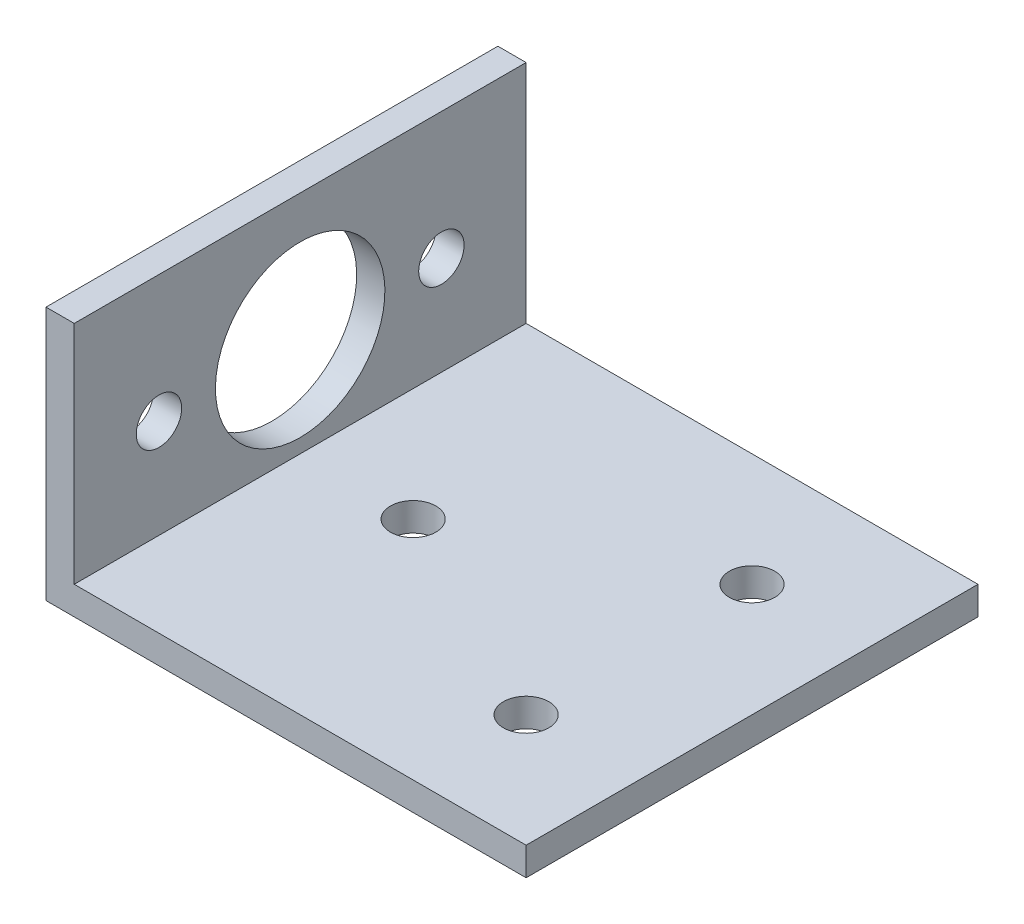
SolidWorks part; units mm, degrees
ref_plane "Front Plane" through (0, 0, 0) normal (0, 0, 1) x (1, 0, 0)
ref_plane "Top Plane" through (0, 0, 0) normal (0, 1, 0) x (1, 0, 0)
ref_plane "Right Plane" through (0, 0, 0) normal (1, 0, 0) x (0, 0, -1)
sketch "Sketch1" plane through (0, 0, 0) normal (0, 0, 1) x (1, 0, 0)
  line L1 (3.175, 50.8) -> (0, 50.8)
  line L2 (3.175, 50.8) -> (3.175, 3.175)
  line L3 (3.175, 0) -> (0, 0)
  line L4 (0, 50.8) -> (0, 0)
  line L5 (3.175, 0) -> (53.975, 0)
  line L7 (3.175, 3.175) -> (53.975, 3.175)
  line L8 (53.975, 0) -> (53.975, 3.175)
  dimension "D1" = 50.8
  dimension "D2" = 50.8
  dimension "D3" = 3.175
  dimension "D4" = 3.175
extrude "Boss-Extrude1" add sketch "Sketch1" along normal blind 50.8
sketch "Sketch2" plane through (0, 0, 0) normal (-1, 0, 0) x (0, 0, 1)
  line L0 (50.8, 0) -> (0, 0) construction
  line L1 (0, 50.8) -> (0, 0) construction
  line L2 (50.8, 50.8) -> (0, 50.8)
  line L3 (50.8, 50.8) -> (50.8, 28.575)
  line L4 (50.8, 28.575) -> (0, 28.575)
  line L5 (0, 50.8) -> (0, 28.575)
  line L6 (25.4, 0) -> (25.4, 28.575) construction
  circle A0 centre (25.4, 14.2875) radius 9.525
  point P4 (25.4, 0)
  dimension "D2" = 19.05
  dimension "D3" = 22.225
extrude "Cut-Extrude1" cut sketch "Sketch2" against normal blind 50.8
sketch "Sketch3" plane through (0, 0, 0) normal (0, -1, 0) x (-1, 0, 0)
  line L0 (0, -50.8) -> (0, 0) construction
  line L1 (-41.275, -38.1) -> (-41.275, -12.7) construction
  circle A0 centre (-15.875, -25.4) radius 2.5527
  circle A1 centre (-41.275, -38.1) radius 2.5527
  circle A2 centre (-41.275, -12.7) radius 2.5527
  point P8 (0, -25.4)
  point P9 (-41.275, -25.4)
  dimension "D1" = 5.1054
  dimension "D2" = 15.875
  dimension "D3" = 41.275
  dimension "D4" = 25.4
extrude "Cut-Extrude2" cut sketch "Sketch3" against normal blind 50.8
sketch "Sketch4" plane through (0, 0, 0) normal (-1, 0, 0) x (0, 0, 1)
  line L0 (25.4, 28.575) -> (25.4, 0) construction
  line L1 (0, 28.575) -> (50.8, 28.575) construction
  line L2 (50.8, 0) -> (0, 0) construction
  line L3 (9.525, 14.2875) -> (41.275, 14.2875) construction
  circle A0 centre (9.525, 14.2875) radius 2.5527
  circle A1 centre (41.275, 14.2875) radius 2.5527
  point P10 (25.4, 14.2875)
  dimension "D1" = 5.1054
  dimension "D2" = 31.75
extrude "Cut-Extrude3" cut sketch "Sketch4" against normal blind 3.175
